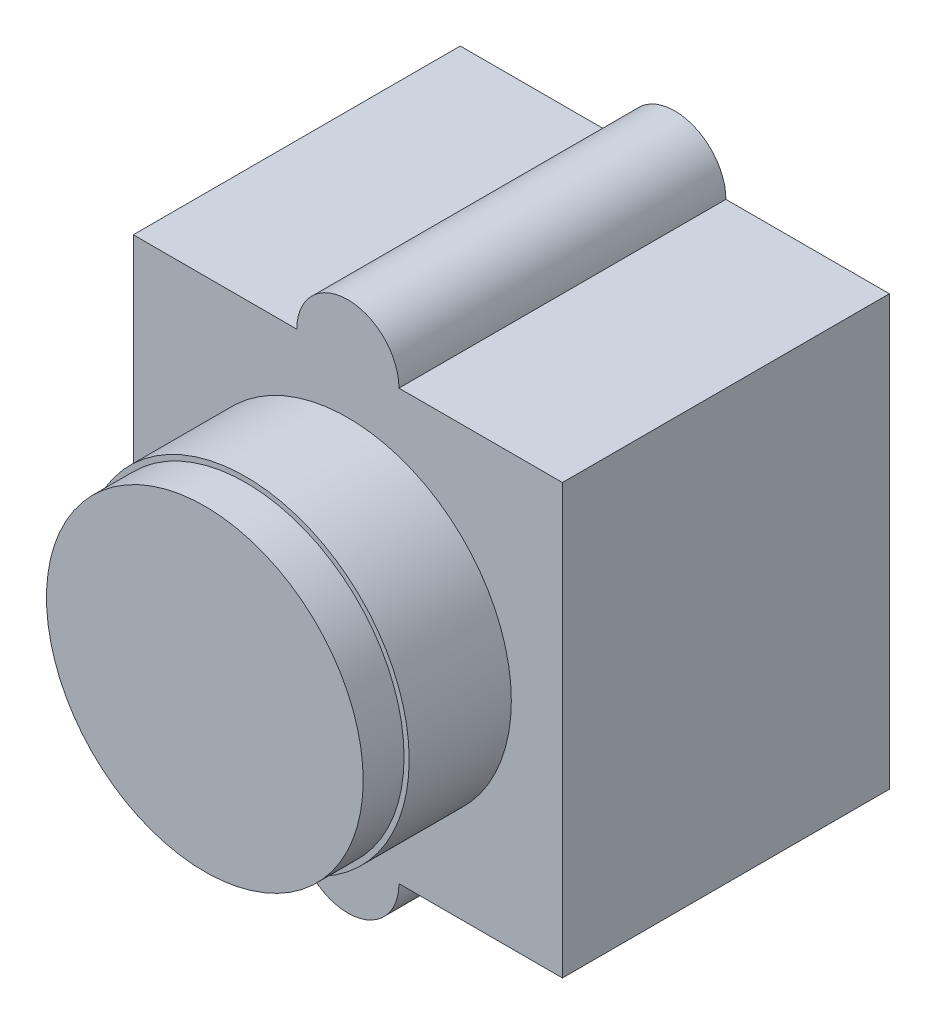
SolidWorks part; units mm, degrees
ref_plane "Front Plane" through (0, 0, 0) normal (0, 0, 1) x (1, 0, 0)
ref_plane "Top Plane" through (0, 0, 0) normal (0, 1, 0) x (1, 0, 0)
ref_plane "Right Plane" through (0, 0, 0) normal (1, 0, 0) x (0, 0, -1)
sketch "Sketch1" plane through (0, 0, 0) normal (0, 0, 1) x (1, 0, 0)
  line L0 (-10.5, -10.5) -> (10.5, 10.5) construction
  line L1 (-10.5, 10.5) -> (-2.5, 10.5)
  line L2 (-10.5, 10.5) -> (-10.5, -10.5)
  line L3 (-10.5, -10.5) -> (-2.5, -10.5)
  line L4 (10.5, 10.5) -> (10.5, -10.5)
  line L5 (0, -13) -> (13.1238, -13) construction
  line L6 (0, 13) -> (18.9421, 13) construction
  line L7 (2.5, -10.5) -> (10.5, -10.5)
  line L8 (2.5, 10.5) -> (10.5, 10.5)
  arc A0 (-2.5, -10.5) -> (2.5, -10.5) centre (0, -10.5) ccw
  arc A1 (2.5, 10.5) -> (-2.5, 10.5) centre (0, 10.5) ccw
  point P4 (0, 0)
  dimension "D3" = 26
  dimension "D4" = 10.5
  dimension "D1" = 21
  dimension "D2" = 21
  dimension "D5" = 10.5
extrude "Extrude1" add sketch "Sketch1" along normal blind 16
sketch "Sketch2" plane through (0, 0, 16) normal (0, 0, 1) x (1, 0, 0)
  circle A0 centre (0, 0) radius 8
  dimension "D1" = 16
extrude "Extrude2" add sketch "Sketch2" along normal blind 5
sketch "Sketch3" plane through (0, 0, 21) normal (0, 0, 1) x (1, 0, 0)
  circle A0 centre (0, 0) radius 7.75
  dimension "D1" = 15.5
extrude "Extrude3" add sketch "Sketch3" along normal blind 2
